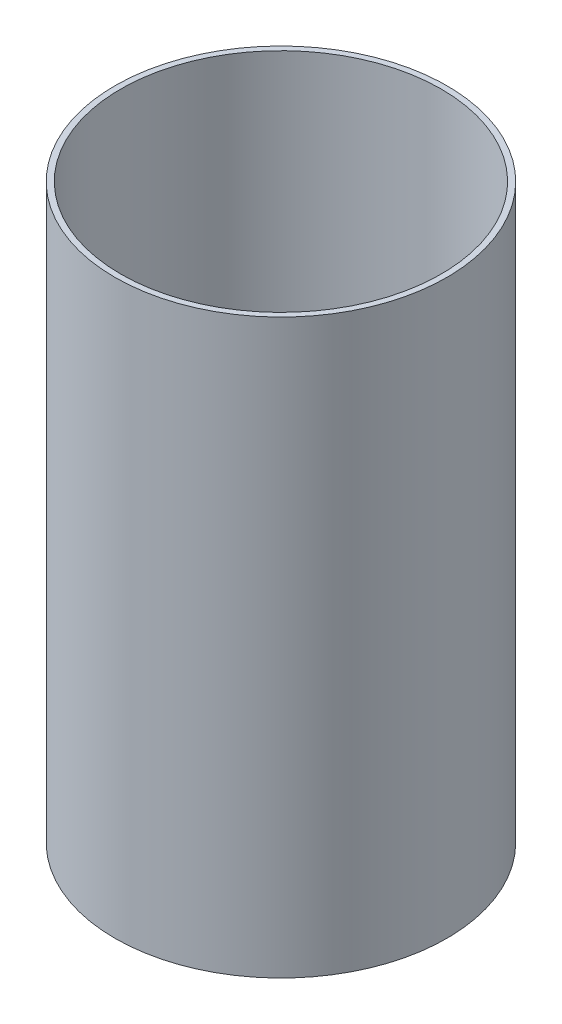
SolidWorks part; units mm, degrees
material "ПВХ Жесткий"
ref_plane "Спереди" through (0, 0, 0) normal (0, 0, 1) x (1, 0, 0)
ref_plane "Сверху" through (0, 0, 0) normal (0, 1, 0) x (1, 0, 0)
ref_plane "Справа" through (0, 0, 0) normal (1, 0, 0) x (0, 0, -1)
sketch "Эскиз1" plane through (0, 0, 0) normal (0, 1, 0) x (1, 0, 0)
  circle A0 centre (0, 0) radius 14.5
  dimension "D1" = 29
extrude "Бобышка-Вытянуть1" add sketch "Эскиз1" along normal blind 50
sketch "Эскиз2" plane through (0, 50, 0) normal (0, 1, 0) x (1, 0, 0)
  circle A0 centre (0, 0) radius 14
  dimension "D1" = 28
extrude "Вырез-Вытянуть1" cut sketch "Эскиз2" against normal blind 49
ref_plane "Плоскость1" through (0, 42, 0) normal (0, 1, 0) x (1, 0, 0)
